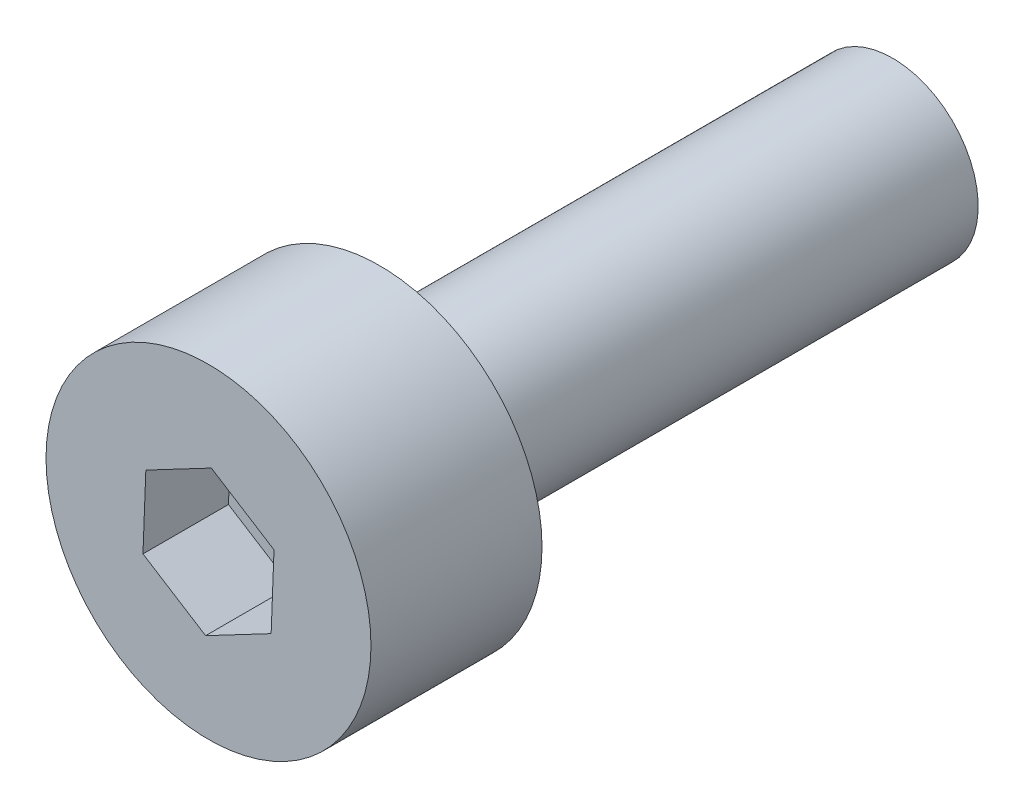
SolidWorks part; units mm, degrees
ref_plane "前视基准面" through (0, 0, 0) normal (0, 0, 1) x (1, 0, 0)
ref_plane "上视基准面" through (0, 0, 0) normal (0, 1, 0) x (1, 0, 0)
ref_plane "右视基准面" through (0, 0, 0) normal (1, 0, 0) x (0, 0, -1)
sketch "草图1" plane through (0, 0, 0) normal (0, 0, 1) x (1, 0, 0)
  circle A0 centre (0, 0) radius 1.9
  dimension "D1" = 3.8
extrude "凸台-拉伸1" add sketch "草图1" along normal blind 2
sketch "草图2" plane through (0, 0, 0) normal (0, 0, -1) x (-1, 0, 0)
  circle A0 centre (0, 0) radius 1
  circle A1 centre (0, 0) radius 1.9
  circle A2 centre (0, 0) radius 1.9
  dimension "D2" = 2
  dimension "D1" = 0
extrude "凸台-拉伸2" add sketch "草图2" along normal blind 6 contours A0
sketch "草图3" plane through (0, 0, 2) normal (0, 0, 1) x (1, 0, 0)
  line L1 (0.7326, -0.4618) -> (0.7662, 0.4036)
  line L2 (0.7662, 0.4036) -> (0.0336, 0.8654)
  line L3 (0.0336, 0.8654) -> (-0.7326, 0.4618)
  line L4 (-0.7326, 0.4618) -> (-0.7662, -0.4036)
  line L5 (-0.7662, -0.4036) -> (-0.0336, -0.8654)
  line L6 (-0.0336, -0.8654) -> (0.7326, -0.4618)
  circle A0 centre (0, 0) radius 0.75 construction
  circle A1 centre (0, 0) radius 1.9
  circle A2 centre (0, 0) radius 1.9
  dimension "D2" = 1.5
  dimension "D1" = 0
extrude "切除-拉伸1" cut sketch "草图3" against normal blind 1 contours L5 L6 L1 L2 L3 L4
